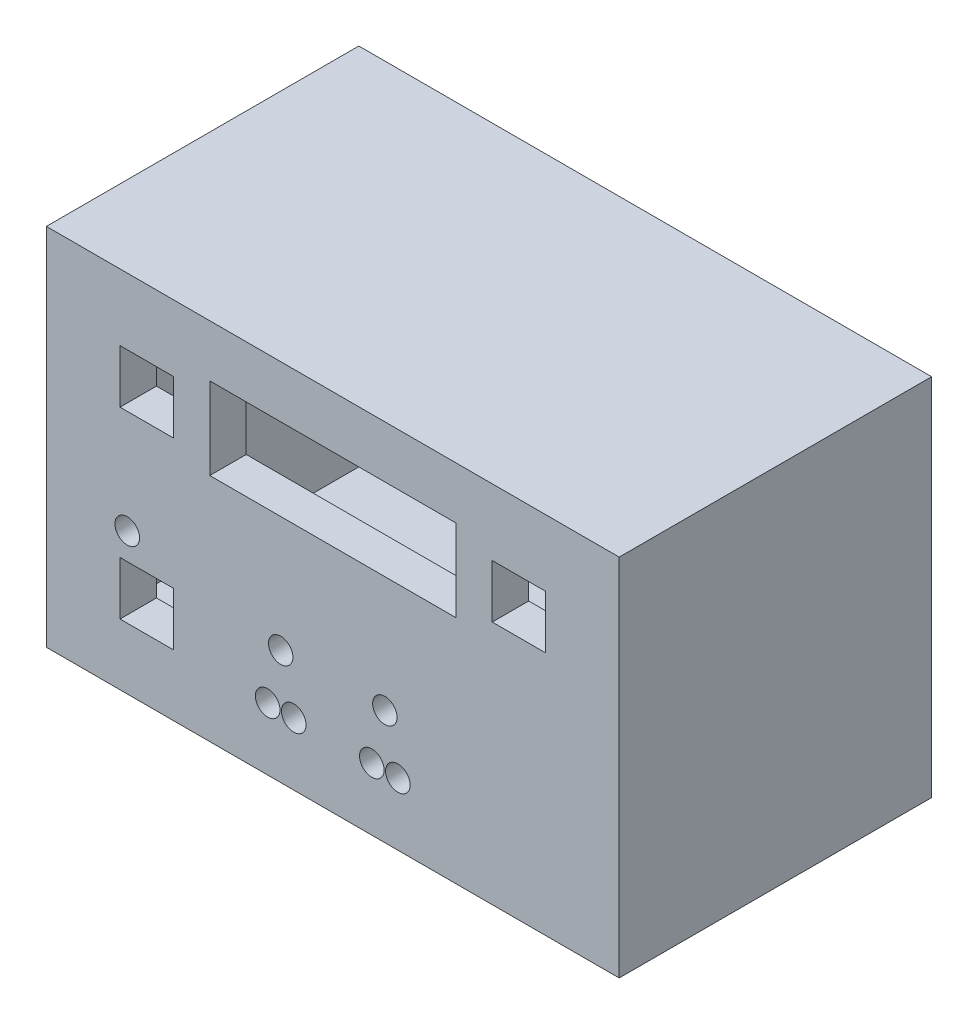
SolidWorks part; units mm, degrees
ref_plane "Front Plane" through (0, 0, 0) normal (0, 0, 1) x (1, 0, 0)
ref_plane "Top Plane" through (0, 0, 0) normal (0, 1, 0) x (1, 0, 0)
ref_plane "Right Plane" through (0, 0, 0) normal (1, 0, 0) x (0, 0, -1)
sketch "Sketch1" plane through (0, 0, 0) normal (0, 0, 1) x (1, 0, 0)
  line L0 (9.525, -29.21) -> (15.875, -29.21) construction
  line L1 (-63.5, -38.1) -> (63.5, -38.1)
  line L2 (-63.5, -38.1) -> (-63.5, 38.1)
  line L3 (-63.5, 38.1) -> (63.5, 38.1)
  line L4 (63.5, -38.1) -> (63.5, 38.1)
  line L5 (-63.5, -38.1) -> (63.5, 38.1) construction
  line L6 (-63.5, 38.1) -> (63.5, -38.1) construction
  line L7 (-30, 31.75) -> (30, 31.75)
  line L8 (-30, 31.75) -> (-30, 11.75)
  line L9 (-30, 11.75) -> (30, 11.75)
  line L10 (30, 31.75) -> (30, 11.75)
  line L11 (-30, 31.75) -> (30, 11.75) construction
  line L12 (-30, 11.75) -> (30, 31.75) construction
  line L13 (-15.875, -29.21) -> (-9.525, -29.21) construction
  line L16 (-51.89, 28.25) -> (-51.89, 15.25)
  line L17 (-51.89, 15.25) -> (-38.89, 15.25)
  line L18 (-38.89, 28.25) -> (-38.89, 15.25)
  line L19 (-51.89, 28.25) -> (-38.89, 15.25) construction
  line L20 (-51.89, 15.25) -> (-38.89, 28.25) construction
  line L24 (-51.89, 28.25) -> (-38.89, 28.25)
  line L25 (38.89, 28.25) -> (38.89, 15.25)
  line L26 (38.89, 15.25) -> (51.89, 15.25)
  line L27 (51.89, 28.25) -> (51.89, 15.25)
  line L28 (38.89, 28.25) -> (51.89, 28.25)
  line L29 (-51.89, -16.4962) -> (-51.89, -29.4962)
  line L30 (-51.89, -29.4962) -> (-38.89, -29.4962)
  line L31 (-38.89, -16.4962) -> (-38.89, -29.4962)
  line L32 (-51.89, -16.4962) -> (-38.89, -16.4962)
  circle A0 centre (-12.7, -16.51) radius 2.9788
  circle A1 centre (12.7, -16.51) radius 2.9788
  circle A2 centre (-15.875, -29.21) radius 3
  circle A3 centre (-9.525, -29.21) radius 3
  circle A4 centre (9.525, -29.21) radius 3
  circle A5 centre (15.875, -29.21) radius 3
  circle A6 centre (-50.1244, -10.0012) radius 3
  point P0 (0, 0)
  point P2 (-12.7, -29.21)
  point P8 (0, 21.75)
  point P18 (12.7, -29.21)
  point P25 (-45.39, 21.75)
  point P39 (-45.39, -16.4962)
  dimension "D1" = 25.4
  dimension "D8" = 6.35
  dimension "D2" = 21.59
  dimension "D3" = 50.8
  dimension "D4" = 50.8
  dimension "D5" = 54.61
  dimension "D6" = 60
  dimension "D7" = 6.35
  dimension "D9" = 6.35
  dimension "D10" = 12.7
  dimension "D11" = 8.89
  dimension "D12" = 13
  dimension "D13" = 20
  dimension "D14" = 8.89
  dimension "D15" = 0
  dimension "D16" = 13
  dimension "D17" = 13
  dimension "D18" = 13
extrude "Boss-Extrude1" add sketch "Sketch1" along normal blind 8.89
sketch "Sketch3" plane through (0, 0, 0) normal (0, 0, -1) x (-1, 0, 0)
  line L20 (36.35, 12.71) -> (54.43, 12.71)
  line L21 (54.43, 12.71) -> (54.43, 30.79)
  line L22 (54.43, 30.79) -> (36.35, 30.79)
  line L23 (36.35, 30.79) -> (36.35, 12.71)
  line L24 (36.35, 12.71) -> (54.43, 12.71)
  line L25 (54.43, 12.71) -> (54.43, 30.79)
  line L26 (54.43, 30.79) -> (36.35, 30.79)
  line L27 (36.35, 30.79) -> (36.35, 12.71)
  line L28 (63.5, -38.1) -> (-63.5, -38.1) construction
  line L29 (63.5, 38.1) -> (63.5, -38.1) construction
  line L30 (-63.5, -38.1) -> (-63.5, 38.1) construction
  line L31 (-63.5, 38.1) -> (63.5, 38.1) construction
  line L32 (36.35, -13.9562) -> (36.35, -32.0362)
  line L33 (36.35, -32.0362) -> (54.43, -32.0362)
  line L34 (54.43, -32.0362) -> (54.43, -13.9562)
  line L35 (54.43, -13.9562) -> (36.35, -13.9562)
  line L36 (-54.43, 12.71) -> (-36.35, 12.71)
  line L37 (-54.43, 30.79) -> (-54.43, 12.71)
  line L38 (-36.35, 30.79) -> (-54.43, 30.79)
  line L39 (-36.35, 12.71) -> (-36.35, 30.79)
  line L40 (-54.43, 12.71) -> (-36.35, 12.71)
  line L41 (-54.43, 30.79) -> (-54.43, 12.71)
  line L42 (-36.35, 30.79) -> (-54.43, 30.79)
  line L43 (-36.35, 12.71) -> (-36.35, 30.79)
  line L48 (32.54, 9.21) -> (32.54, 34.29)
  line L49 (32.54, 34.29) -> (-32.54, 34.29)
  line L50 (-32.54, 34.29) -> (-32.54, 9.21)
  line L51 (-32.54, 9.21) -> (32.54, 9.21)
  line L52 (32.54, 9.21) -> (32.54, 34.29)
  line L53 (32.54, 34.29) -> (-32.54, 34.29)
  line L54 (-32.54, 34.29) -> (-32.54, 9.21)
  line L55 (-32.54, 9.21) -> (32.54, 9.21)
  line L56 (36.35, -13.9562) -> (36.35, -32.0362)
  line L57 (36.35, -32.0362) -> (54.43, -32.0362)
  line L58 (54.43, -32.0362) -> (54.43, -13.9562)
  line L59 (54.43, -13.9562) -> (36.35, -13.9562)
  line L60 (63.5, -38.1) -> (-63.5, -38.1)
  line L61 (63.5, 38.1) -> (63.5, -38.1)
  line L62 (-63.5, -38.1) -> (-63.5, 38.1)
  line L63 (-63.5, 38.1) -> (63.5, 38.1)
  circle A1052 centre (12.7, -16.51) radius 5.5188
  circle A1053 centre (12.7, -16.51) radius 5.5188
  circle A1055 centre (15.875, -29.21) radius 5.54
  circle A1056 centre (15.875, -29.21) radius 5.54
  circle A1058 centre (9.525, -29.21) radius 5.54
  circle A1059 centre (9.525, -29.21) radius 5.54
  circle A1061 centre (-9.525, -29.21) radius 5.54
  circle A1062 centre (-9.525, -29.21) radius 5.54
  circle A1064 centre (-15.875, -29.21) radius 5.54
  circle A1065 centre (-15.875, -29.21) radius 5.54
  circle A1067 centre (-12.7, -16.51) radius 5.5188
  circle A1068 centre (-12.7, -16.51) radius 5.5188
  dimension "D2" = 2.54
  dimension "D3" = 2.54
  dimension "D4" = 2.54
  dimension "D5" = 2.54
  dimension "D6" = 2.54
  dimension "D7" = 2.54
  dimension "D8" = 2.54
  dimension "D9" = 2.54
  dimension "D10" = 2.54
  dimension "D11" = 2.54
extrude "Cut-Extrude1" cut sketch "Sketch3" against normal blind 3.81
sketch "Sketch5" plane through (0, 0, 8.89) normal (0, 0, 1) x (1, 0, 0)
  line L0 (69.85, 44.45) -> (-69.85, 44.45)
  line L1 (-69.85, 44.45) -> (-69.85, -44.45)
  line L2 (-69.85, -44.45) -> (69.85, -44.45)
  line L3 (69.85, -44.45) -> (69.85, 44.45)
  line L4 (63.5, -38.1) -> (63.5, 38.1)
  line L5 (63.5, 38.1) -> (-63.5, 38.1)
  line L6 (-63.5, 38.1) -> (-63.5, -38.1)
  line L7 (-63.5, -38.1) -> (63.5, -38.1)
  line L8 (63.5, -38.1) -> (63.5, 38.1)
  line L9 (63.5, 38.1) -> (-63.5, 38.1)
  line L10 (-63.5, 38.1) -> (-63.5, -38.1)
  line L11 (-63.5, -38.1) -> (63.5, -38.1)
  line L12 (64.77, -39.37) -> (64.77, 39.37)
  line L13 (64.77, 39.37) -> (-64.77, 39.37)
  line L14 (-64.77, 39.37) -> (-64.77, -39.37)
  line L15 (-64.77, -39.37) -> (64.77, -39.37)
  line M21 (63.5, -38.1) -> (63.5, 38.1)
  line M22 (63.5, 38.1) -> (-63.5, 38.1)
  line M23 (-63.5, 38.1) -> (-63.5, -38.1)
  line M24 (-63.5, -38.1) -> (63.5, -38.1)
  dimension "D1" = 0
  dimension "D2" = 6.35
  dimension "D3" = 1.27
extrude "Boss-Extrude2" add sketch "Sketch5" against normal up to vertex contours L14 L15 L12 L13 M21 M24 M23 M22
sketch "Sketch6" plane through (0, 0, 8.89) normal (0, 0, 1) x (1, 0, 0)
  line L0 (-69.85, -44.45) -> (69.85, -44.45)
  line L1 (69.85, -44.45) -> (69.85, 44.45)
  line L2 (69.85, 44.45) -> (-69.85, 44.45)
  line L3 (-69.85, 44.45) -> (-69.85, -44.45)
  line L4 (-64.77, 39.37) -> (-64.77, -39.37)
  line L5 (-64.77, -39.37) -> (64.77, -39.37)
  line L6 (64.77, -39.37) -> (64.77, 39.37)
  line L7 (64.77, 39.37) -> (-64.77, 39.37)
  line L8 (-64.77, 39.37) -> (-64.77, -39.37)
  line L9 (-64.77, -39.37) -> (64.77, -39.37)
  line L10 (64.77, -39.37) -> (64.77, 39.37)
  line L11 (64.77, 39.37) -> (-64.77, 39.37)
  dimension "D1" = 0
  dimension "D2" = 5.08
extrude "Boss-Extrude3" add sketch "Sketch6" against normal blind 76.2
sketch "Sketch7" plane through (-69.85, 0, 0) normal (-1, 0, 0) x (0, 0, 1)
  line L0 (3.81, 39.37) -> (3.81, -39.37) construction
  line L1 (3.81, 39.37) -> (3.81, -39.37)
  line L3 (3.81, -3.6377) -> (-3.1427, -3.6377)
  line L4 (8.89, -44.45) -> (8.89, 44.45)
  line L5 (8.89, 44.45) -> (-67.31, 44.45)
  line L6 (-67.31, 44.45) -> (-67.31, -44.45)
  line L7 (-67.31, -44.45) -> (8.89, -44.45)
  line L8 (8.89, -44.45) -> (8.89, 44.45)
  line L9 (8.89, 44.45) -> (-67.31, 44.45)
  line L10 (-67.31, 44.45) -> (-67.31, -44.45)
  line L11 (-67.31, -44.45) -> (8.89, -44.45)
  line L12 (3.81, -3.6377) -> (3.81, 6.6833)
  line L13 (3.81, 6.6833) -> (-3.1427, 6.6833)
  line L14 (-3.1427, -3.6377) -> (-3.1427, 6.6833)
  dimension "D1" = 0
extrude "Cut-Extrude3" cut sketch "Sketch7" against normal up to next contours L14 L3 L1 L13
